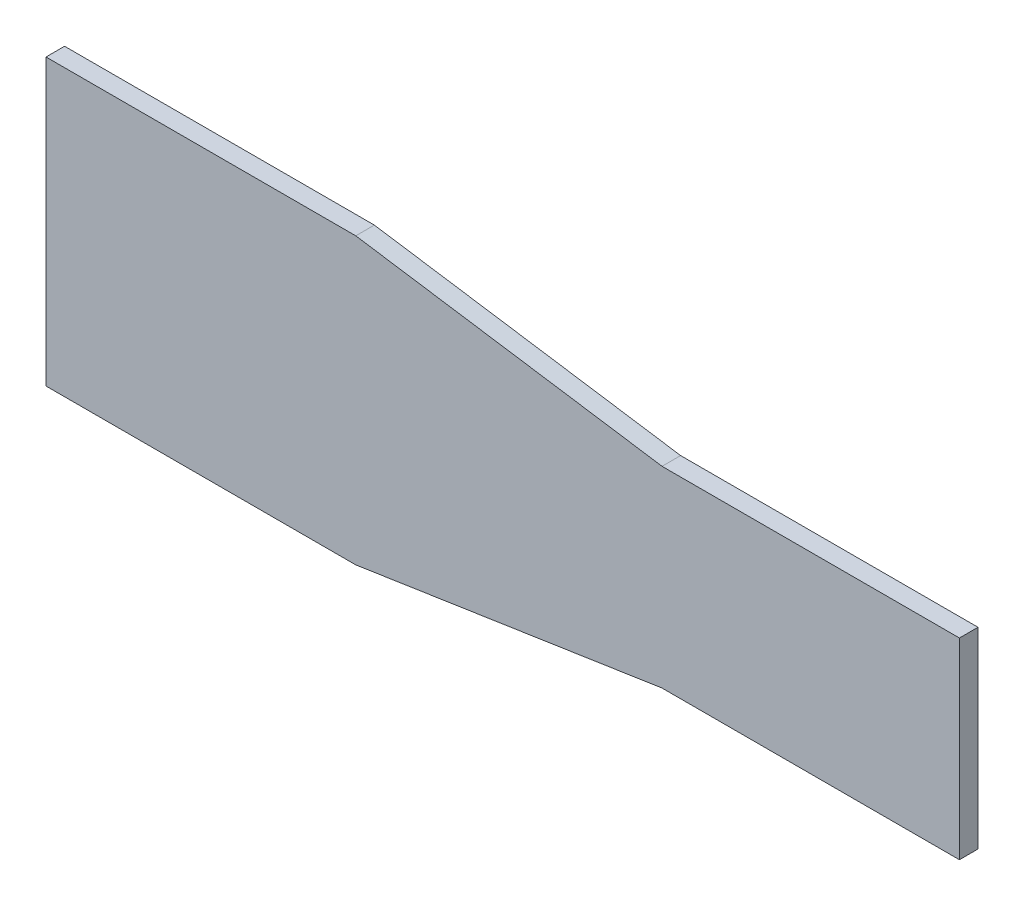
SolidWorks part; units mm, degrees
ref_plane "Plan de face" through (0, 0, 0) normal (0, 0, 1) x (1, 0, 0)
ref_plane "Plan de dessus" through (0, 0, 0) normal (0, 1, 0) x (1, 0, 0)
ref_plane "Plan de droite" through (0, 0, 0) normal (1, 0, 0) x (0, 0, -1)
sketch "Esquisse1" plane through (0, 0, 0) normal (0, 0, 1) x (1, 0, 0)
  line L0 (0, 15.5) -> (-49.4343, 23)
  line L1 (-48, 15.5) -> (48, 15.5) construction
  line L2 (-48, 15.5) -> (-48, -15.5) construction
  line L3 (-48, -15.5) -> (48, -15.5) construction
  line L4 (48, 15.5) -> (48, -15.5)
  line L5 (-48, 15.5) -> (48, -15.5) construction
  line L6 (-48, -15.5) -> (48, 15.5) construction
  line L8 (-49.4343, -23) -> (0, -15.5)
  line L9 (0, 15.5) -> (48, 15.5)
  line L10 (0, -15.5) -> (48, -15.5)
  line L11 (-49.4343, 23) -> (-99.4343, 23)
  line L12 (-99.4343, 23) -> (-99.4343, -23)
  line L13 (-99.4343, -23) -> (-49.4343, -23)
  point P0 (0, 0)
  dimension "D1" = 96
  dimension "D2" = 31
  dimension "D3" = 50
  dimension "D4" = 46
  dimension "D5" = 50
  dimension "D6" = 7.5
extrude "Boss.-Extru.1" add sketch "Esquisse1" along normal blind 3
